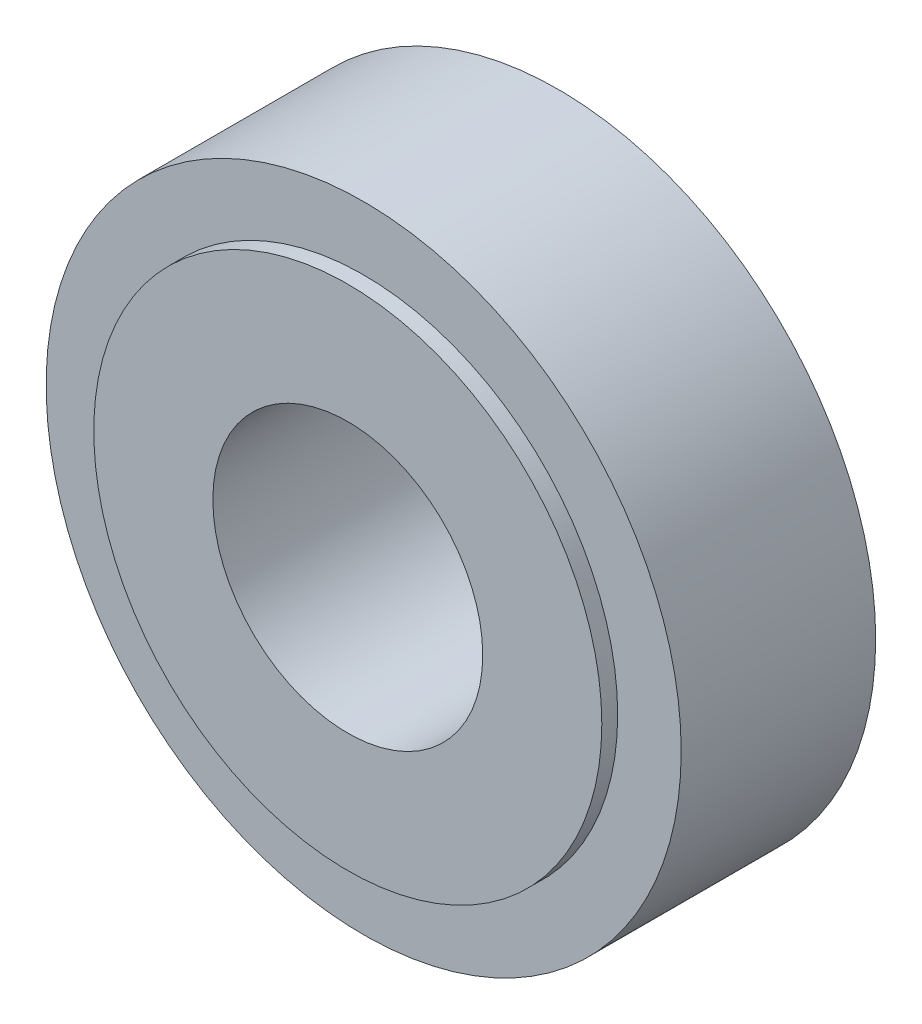
SolidWorks part; units mm, degrees
material "1023 Tôle d'acier au carbone (SS)"
ref_plane "Plan de face" through (0, 0, 0) normal (0, 0, 1) x (1, 0, 0)
ref_plane "Plan de dessus" through (0, 0, 0) normal (0, 1, 0) x (1, 0, 0)
ref_plane "Plan de droite" through (0, 0, 0) normal (1, 0, 0) x (0, 0, -1)
sketch "Esquisse1" plane through (0, 0, 0) normal (0, 0, 1) x (1, 0, 0)
  circle A0 centre (0, 0) radius 20
  circle A1 centre (0, 0) radius 8.5
  dimension "D1" = 17
  dimension "D2" = 40
extrude "Boss.-Extru.1" add sketch "Esquisse1" along normal blind 13.25
sketch "Esquisse2" plane through (0, 0, 0) normal (0, 0, -1) x (-1, 0, 0)
  circle A0 centre (0, 0) radius 17
  circle A1 centre (0, 0) radius 20 construction
  dimension "D1" = 3
extrude "Enlèv. mat.-Extru.1" cut sketch "Esquisse2" against normal blind 1
sketch "Esquisse3" plane through (0, 0, 13.25) normal (0, 0, 1) x (1, 0, 0)
  circle A0 centre (0, 0) radius 16
  circle A1 centre (0, 0) radius 20 construction
  dimension "D1" = 4
extrude "Enlèv. mat.-Extru.2" cut sketch "Esquisse3" against normal blind 1 flip side to cut
